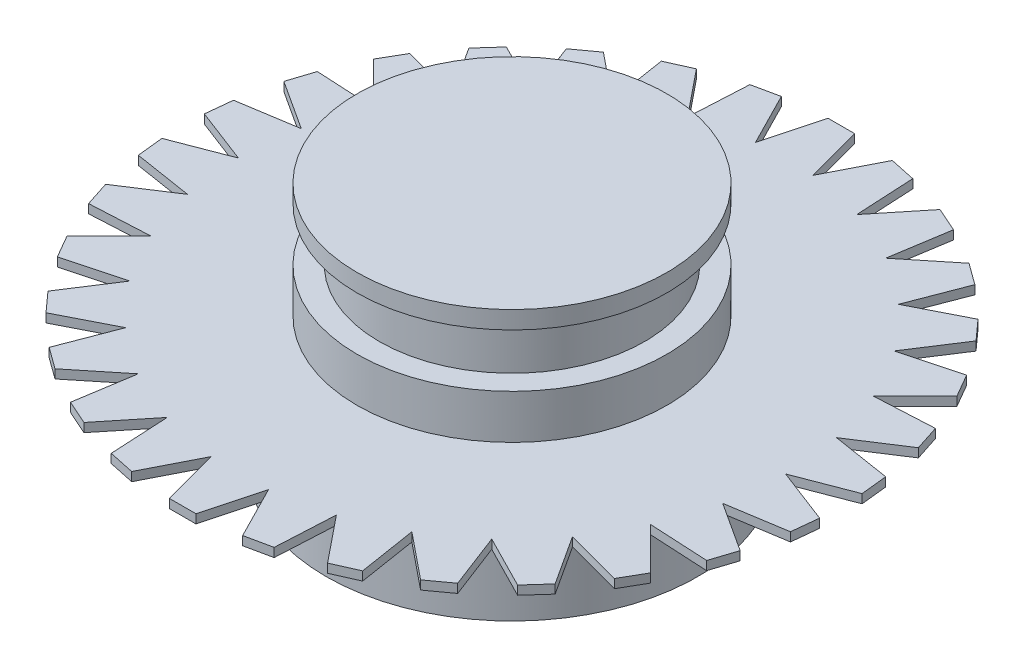
SolidWorks part; units mm, degrees
ref_plane "Front Plane" through (0, 0, 0) normal (0, 0, 1) x (1, 0, 0)
ref_plane "Top Plane" through (0, 0, 0) normal (0, 1, 0) x (1, 0, 0)
ref_plane "Right Plane" through (0, 0, 0) normal (1, 0, 0) x (0, 0, -1)
sketch "Sketch1" plane through (0, 0, 0) normal (0, 1, 0) x (1, 0, 0)
  circle A0 centre (0, 0) radius 30
  dimension "D1" = 60
extrude "Tandhjul mainBody" add sketch "Sketch1" along normal blind 1 contours A0
sketch "Sketch2" plane through (0, 1, 0) normal (0, 1, 0) x (1, 0, 0)
  circle A0 centre (0, 0) radius 15
  dimension "D1" = 30
extrude "Tandhjul fiskelinie" add sketch "Sketch2" along normal blind 20 contours A0
sketch "Sketch3" plane through (0, 21, 0) normal (0, 1, 0) x (1, 0, 0)
  circle A0 centre (0, 0) radius 17.5
  dimension "D1" = 35
extrude "Tandhjul fiskelinieStopper" add sketch "Sketch3" along normal blind 1 contours A0
sketch "Sketch9" plane through (0, 1, 0) normal (0, 1, 0) x (1, 0, 0)
  line L4 (0, 0) -> (0, 33.6294)
  line L5 (0, 0) -> (32.8619, 0)
  line L6 (32.8619, 0) -> (0, 0)
  line L7 (-5.0381, 23.9926) -> (5.0381, 23.9926)
  line L9 (1.5, 37.1971) -> (-1.5, 37.1971)
  line L10 (-1.5, 37.1971) -> (-5.0381, 23.9926)
  line L11 (1.5, 37.1971) -> (5.0381, 23.9926)
  point P3 (0, 23.9926)
  dimension "D1" = 0
  dimension "D2" = 3
  dimension "D3" = 105
  dimension "D4" = 105
  dimension "D5" = 75
  dimension "D6" = 75
extrude "Tænder" add sketch "Sketch9" against normal blind 1
pattern_circular "TænderPattern" count 30 over 360 about axis through (0, 0, 0) along (0, 1, 0) of "Tænder"
sketch "Sketch11" plane through (0, 1, 0) normal (0, 1, 0) x (1, 0, 0)
  circle A0 centre (0, 0) radius 17.5
  dimension "D1" = 35
extrude "Boss-Extrude1" add sketch "Sketch11" along normal blind 5
sketch "Sketch12" plane through (0, 0, 0) normal (0, -1, 0) x (1, 0, 0)
  circle A0 centre (0, 0) radius 21
  dimension "D1" = 42
extrude "Boss-Extrude2" add sketch "Sketch12" along normal blind 14 contours A0
fillet "Fillet1" radius 2 1 edges at (0, 0, 21)
sketch "Sketch13" plane through (0, -14, 0) normal (0, -1, 0) x (1, 0, 0)
  circle A0 centre (0, 0) radius 18.5
  dimension "D1" = 37
extrude "Cut-Extrude1" cut sketch "Sketch13" against normal blind 12
sketch "Sketch14" plane through (0, -2, 0) normal (0, -1, 0) x (1, 0, 0)
  circle A0 centre (0, 0) radius 17
  dimension "D1" = 34
extrude "Cut-Extrude2" cut sketch "Sketch14" against normal blind 2
sketch "Sketch15" plane through (0, 22, 0) normal (0, 1, 0) x (1, 0, 0)
  circle A0 centre (-1.0245, -1.0989) radius 23.6797
extrude "Cut-Extrude3" cut sketch "Sketch15" against normal blind 10
sketch "Sketch16" plane through (0, 12, 0) normal (0, 1, 0) x (1, 0, 0)
ref_plane "Plane1" through (0, 12, 0) normal (0, 1, 0) x (1, 0, 0)
sketch "Sketch18" plane through (0, 12, 0) normal (0, 1, 0) x (1, 0, 0)
  circle A0 centre (0, 0) radius 17.5
  dimension "D1" = 35
extrude "Boss-Extrude3" add sketch "Sketch18" along normal blind 2
